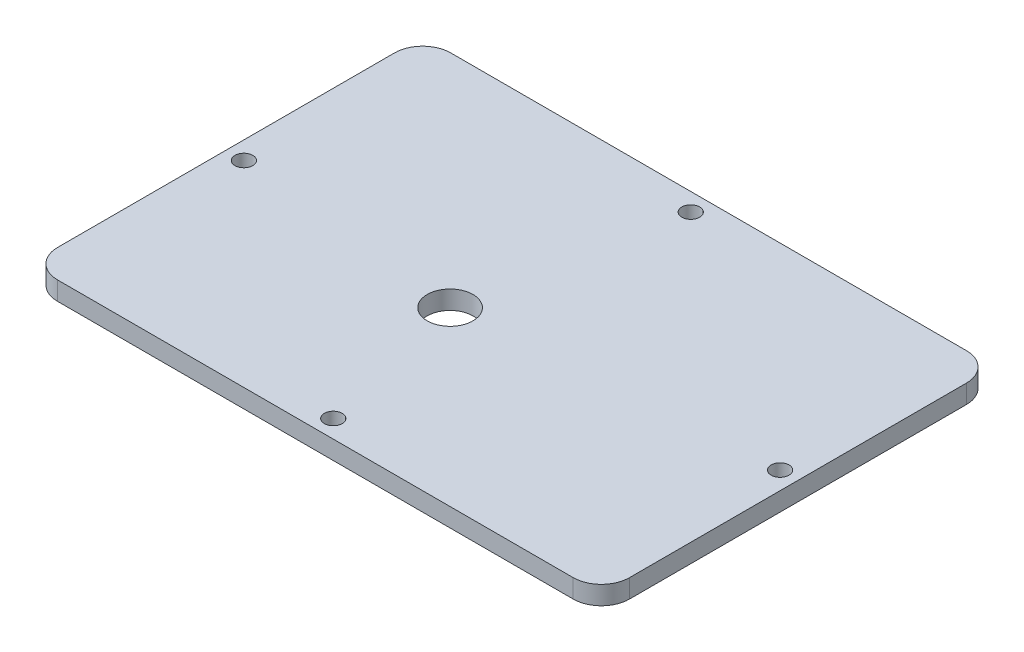
SolidWorks part; units mm, degrees
material "UHMW"
ref_plane "Front Plane" through (0, 0, 0) normal (0, 0, 1) x (1, 0, 0)
ref_plane "Top Plane" through (0, 0, 0) normal (0, 1, 0) x (1, 0, 0)
ref_plane "Right Plane" through (0, 0, 0) normal (1, 0, 0) x (0, 0, -1)
sketch "Sketch1" plane through (0, 0, 0) normal (0, 1, 0) x (1, 0, 0)
  line L1 (-50.8, -34.925) -> (50.8, -34.925)
  line L2 (-50.8, -34.925) -> (-50.8, 34.925)
  line L3 (-50.8, 34.925) -> (50.8, 34.925)
  line L4 (50.8, -34.925) -> (50.8, 34.925)
  line L5 (-50.8, -34.925) -> (50.8, 34.925) construction
  line L6 (-50.8, 34.925) -> (50.8, -34.925) construction
  point P0 (0, 0)
  dimension "D1" = 101.6
  dimension "D2" = 69.85
extrude "Boss-Extrude1" add sketch "Sketch1" along normal blind 3.302
sketch "Sketch4" plane through (0, 0, 0) normal (0, -1, 0) x (-1, 0, 0)
  circle A0 centre (0, 31.75) radius 1.5875
  circle A1 centre (-47.625, 0) radius 1.5875
  circle A2 centre (0, -31.75) radius 1.5875
  circle A3 centre (47.625, 0) radius 1.5875
  circle A8 centre (-47.625, 0) radius 1.5875 construction
  circle A9 centre (0, 31.75) radius 1.5875 construction
  circle A10 centre (0, -31.75) radius 1.5875 construction
  circle A11 centre (47.625, 0) radius 1.5875 construction
extrude "Cut-Extrude1" cut sketch "Sketch4" against normal through all
fillet "Fillet1" radius 5 4 edges at (50.8, 1.651, -34.925) (50.8, 1.651, 34.925) (-50.8, 1.651, 34.925) (-50.8, 1.651, -34.925)
sketch "Sketch5" plane through (0, 3.302, 0) normal (0, 1, 0) x (1, 0, 0)
  circle A0 centre (-6.6714, -4.3283) radius 4.064
  circle A2 centre (-6.6714, -4.3283) radius 4.064 construction
extrude "Cut-Extrude2" cut sketch "Sketch5" against normal through all
